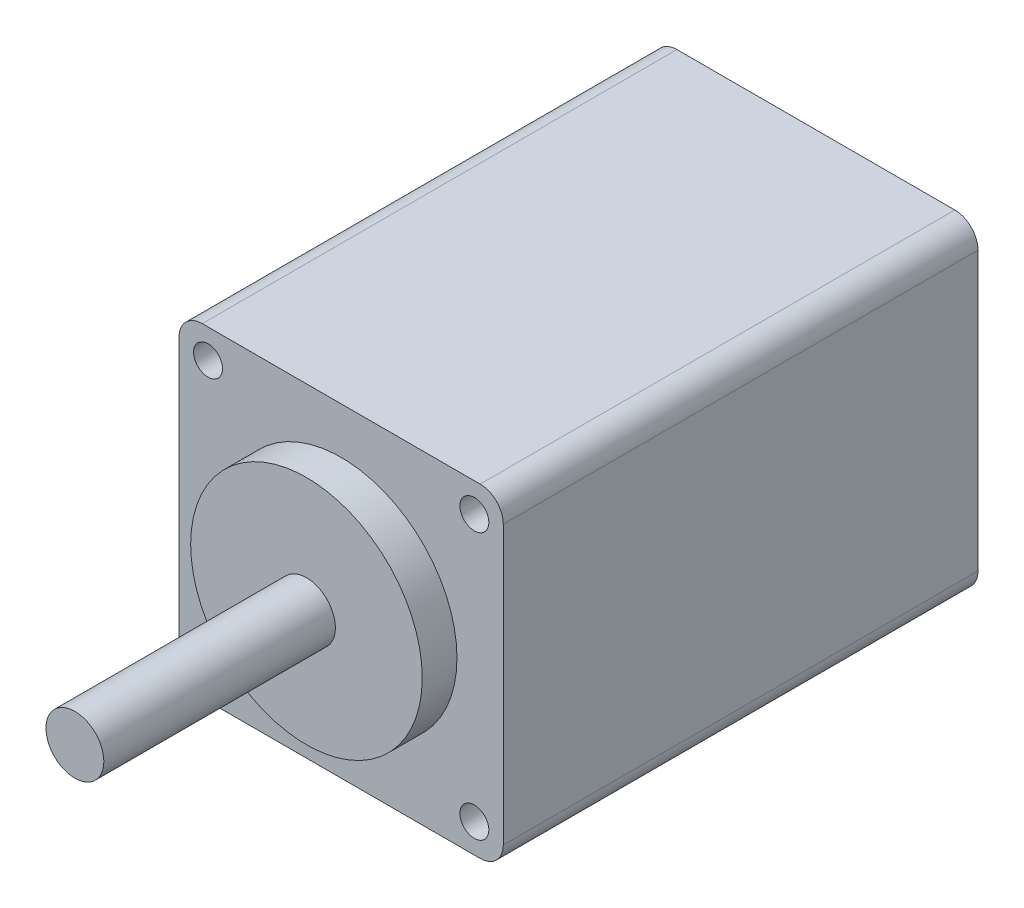
SolidWorks part; units mm, degrees
ref_plane "前视基准面" through (0, 0, 0) normal (0, 0, 1) x (1, 0, 0)
ref_plane "上视基准面" through (0, 0, 0) normal (0, 1, 0) x (1, 0, 0)
ref_plane "右视基准面" through (0, 0, 0) normal (1, 0, 0) x (0, 0, -1)
sketch "草图1" plane through (0, 0, 0) normal (0, 0, 1) x (1, 0, 0)
  line L0 (-14, 0) -> (14, 0) construction
  line L1 (-14, 14) -> (14, 14)
  line L2 (-14, 14) -> (-14, -14)
  line L3 (-14, -14) -> (14, -14)
  line L4 (14, 14) -> (14, -14)
  line L5 (-14, 14) -> (14, -14) construction
  line L6 (-14, -14) -> (14, 14) construction
  line L7 (0, 14) -> (0, -14) construction
  circle A0 centre (-11.5, 11.5) radius 1.25
  circle A2 centre (11.5, 11.5) radius 1.25
  circle A3 centre (11.5, -11.5) radius 1.25
  circle A4 centre (-11.5, -11.5) radius 1.25
  point P0 (0, 0)
  dimension "D3" = 2.5
  dimension "D4" = 23
  dimension "D1" = 28
  dimension "D2" = 28
extrude "凸台-拉伸1" add sketch "草图1" along normal blind 41
sketch "草图2" plane through (0, 0, 41) normal (0, 0, 1) x (1, 0, 0)
  circle A0 centre (0, 0) radius 10
  dimension "D1" = 20
extrude "凸台-拉伸2" add sketch "草图2" along normal blind 3
sketch "草图3" plane through (0, 0, 44) normal (0, 0, 1) x (1, 0, 0)
  circle A0 centre (0, 0) radius 2.5
  dimension "D1" = 5
extrude "凸台-拉伸3" add sketch "草图3" along normal blind 20
fillet "圆角1" radius 2 4 edges at (-14, -14, 20.5) (14, -14, 20.5) (14, 14, 20.5) (-14, 14, 20.5)
sketch "草图4" plane through (0, 0, 64) normal (0, 0, 1) x (1, 0, 0)
  circle A0 centre (0, 0) radius 1.0594 construction
